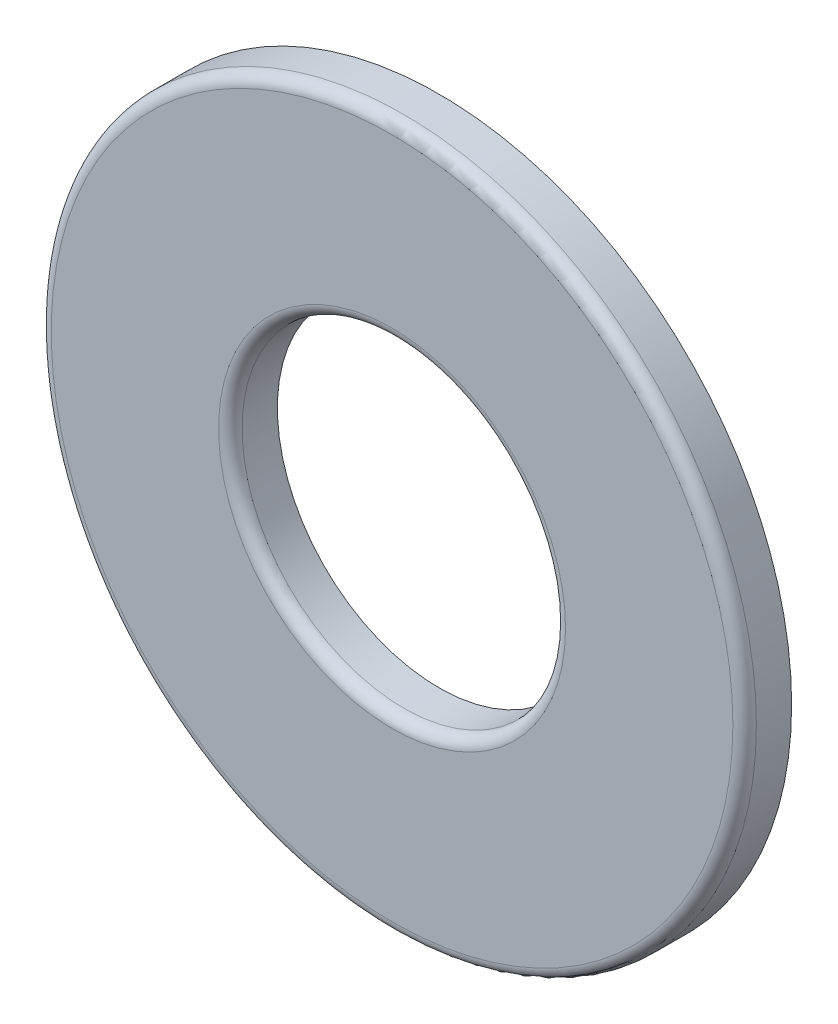
SolidWorks part; units mm, degrees
other "Imported1" parameters "D1"=0.3175, "TH"=1.0287, "Thickness"=1.27
ref_plane "Front Plane" through (0, 0, 0) normal (0, 0, 1) x (1, 0, 0)
ref_plane "Top Plane" through (0, 0, 0) normal (0, 1, 0) x (1, 0, 0)
ref_plane "Right Plane" through (0, 0, 0) normal (1, 0, 0) x (0, 0, -1)
sketch "Sketch1" plane through (0, 0, 0) normal (0, 0, 1) x (1, 0, 0)
  line L0 (-9.525, 0) -> (9.525, 0) construction
  line L1 (-4.3688, 0) -> (4.3688, 0) construction
  circle A0 centre (0, 0) radius 4.3688 construction
  circle A1 centre (0, 0) radius 9.525 construction
  point P8 (0, 0)
  point P9 (0, 9.525)
  point P11 (4.3688, 0)
  dimension "ID" = 8.7376
  dimension "OD" = 19.05
sketch "Sketch2" plane through (0, 0, 0) normal (1, 0, 0) x (0, 0, -1)
  line L0 (-0.635, 9.525) -> (0.635, 9.525) construction
  point P2 (0, 9.525)
sketch "Sketch3" plane through (0, 0, 0) normal (0, 0, 1) x (1, 0, 0)
  circle A0 centre (0, 0) radius 4.3688
  circle A1 centre (0, 0) radius 9.525
extrude "Boss-Extrude1" add sketch "Sketch3" along normal up to vertex (0.635 mm away) and the other way up to vertex (0.635 mm away) up to point (0, 9.525, 0.635) other way up to point (0, 9.525, -0.635)
fillet "Fillet1" radius 0.3175 2 edges at (9.525, 0, 0.635) (4.3688, 0, 0.635)
equation "\"D1@Fillet1\"=\"Thickness@Sketch2\"/4"
